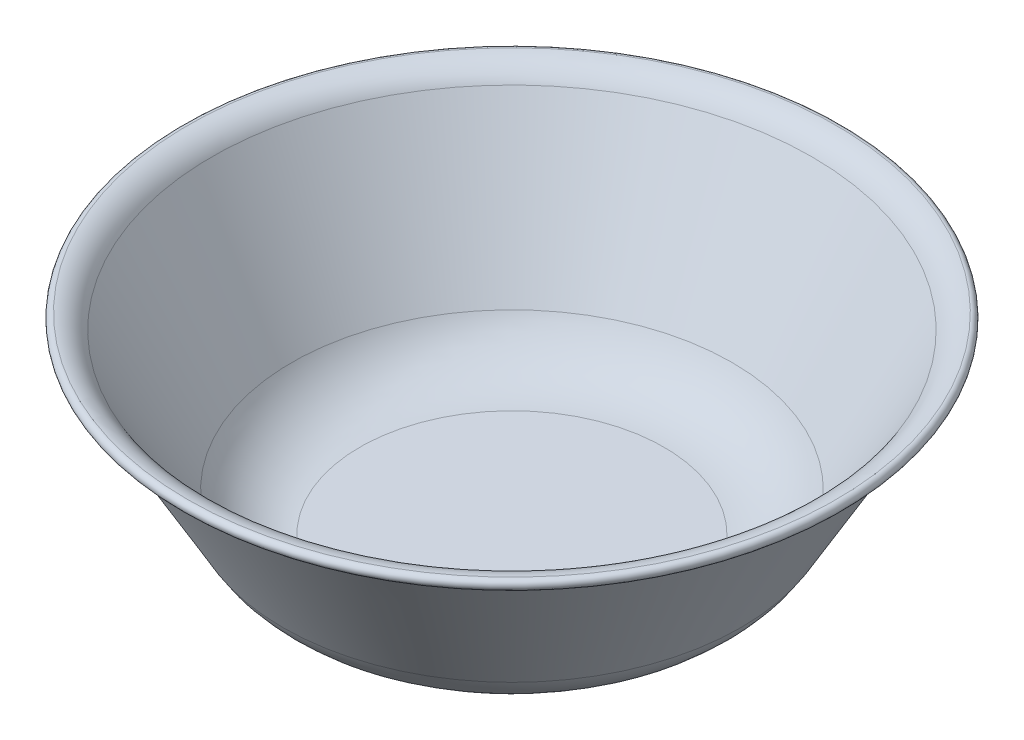
SolidWorks part; units mm, degrees
ref_plane "Front Plane" through (0, 0, 0) normal (0, 0, 1) x (1, 0, 0)
ref_plane "Top Plane" through (0, 0, 0) normal (0, 1, 0) x (1, 0, 0)
ref_plane "Right Plane" through (0, 0, 0) normal (1, 0, 0) x (0, 0, -1)
sketch "Sketch1" plane through (0, 0, 0) normal (0, 0, 1) x (1, 0, 0)
  line L0 (0, 0) -> (60, 0)
  line L1 (90.3109, 17.5) -> (121.7914, 72.0259)
  line L2 (0, 0) -> (0, 96.6256) construction
  line L3 (0, 4) -> (60, 4)
  line L4 (86.8468, 19.5) -> (118.3273, 74.0259)
  line L5 (0, 4) -> (0, 0)
  arc A0 (90.3109, 17.5) -> (60, 0) centre (60, 35) cw
  arc A1 (128.1439, 76.0052) -> (121.7914, 72.0259) centre (128.7197, 68.0259) ccw
  arc A2 (128.1439, 76.0052) -> (127.8561, 79.9948) centre (128, 78) ccw
  arc A3 (86.8468, 19.5) -> (60, 4) centre (60, 35) cw
  arc A4 (127.8561, 79.9948) -> (118.3273, 74.0259) centre (128.7197, 68.0259) ccw
  dimension "D4" = 35
  dimension "D3" = 8
  dimension "D5" = 4
  dimension "D6" = 78
  dimension "D1" = 60
  dimension "D2" = 30
  dimension "D7" = 128
revolve "Revolve1" add sketch "Sketch1" angle 360 about L5
scale "Scale1" scale about centroid uniform scaling yes scale factor 0.5
